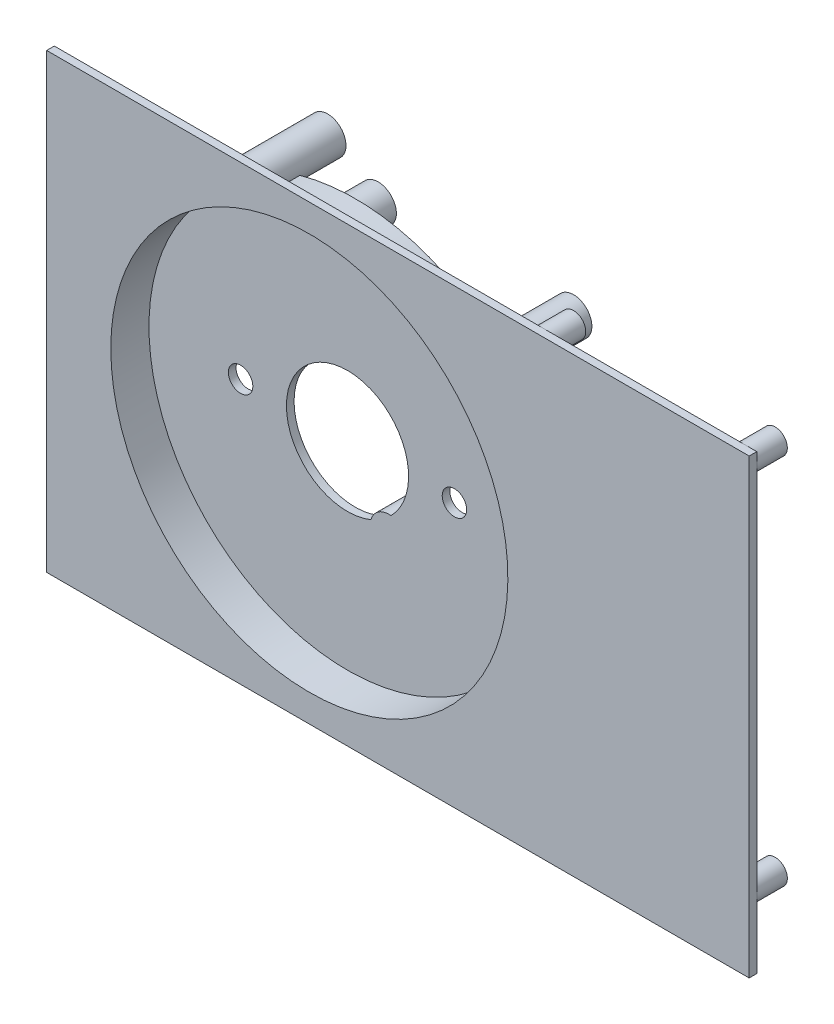
SolidWorks part; units mm, degrees
ref_plane "Front Plane" through (0, 0, 0) normal (0, 0, 1) x (1, 0, 0)
ref_plane "Top Plane" through (0, 0, 0) normal (0, 1, 0) x (1, 0, 0)
ref_plane "Right Plane" through (0, 0, 0) normal (1, 0, 0) x (0, 0, -1)
sketch "Sketch1" plane through (0, 0, 7.9375) normal (0, 0, -1) x (-1, 0, 0)
  line L1 (54.61, -46.99) -> (-91.44, -46.99)
  line L2 (54.61, -46.99) -> (54.61, 46.99)
  line L3 (54.61, 46.99) -> (-91.44, 46.99)
  line L4 (-91.44, -46.99) -> (-91.44, 46.99)
  circle A0 centre (0, 0) radius 7.9336 construction
  circle A1 centre (0, 0) radius 12.7 construction
  circle A2 centre (0, 0) radius 41.275 construction
  circle A3 centre (0, 0) radius 41.275
  point P10 (-91.44, 0)
  dimension "D3" = 146.05
  dimension "D1" = 91.44
  dimension "D2" = 93.98
extrude "main" add sketch "Sketch1" along normal blind 1.5875
sketch "Sketch2" plane through (0, 0, 0) normal (0, 0, -1) x (-1, 0, 0)
  circle A0 centre (0, 0) radius 41.275
  circle A1 centre (0, 0) radius 41.275 construction
  circle A2 centre (22.225, 0) radius 2.54
  circle A3 centre (-22.225, 0) radius 2.54
  circle A4 centre (22.225, 0) radius 2.54 construction
  circle A5 centre (-22.225, 0) radius 2.54 construction
  circle A6 centre (0, 0) radius 12.7
  circle A7 centre (0, 0) radius 12.7 construction
extrude "disk top" add sketch "Sketch2" along normal blind 1.5875 separate body
sketch "Sketch3" plane through (0, 0, -1.5875) normal (0, 0, -1) x (-1, 0, 0)
  circle A0 centre (0, 0) radius 41.275 construction
  circle A1 centre (0, 0) radius 41.275
  circle A2 centre (0, 0) radius 42.8625
  dimension "D1" = 1.5875
extrude "raised disk" add sketch "Sketch3" against normal up to next
sketch "Sketch4" plane through (0, 0, 6.35) normal (0, 0, -1) x (-1, 0, 0)
  circle A0 centre (15.24, 41.91) radius 3.81
  circle A1 centre (15.24, -44.45) radius 3.81
  circle A2 centre (15.24, -44.45) radius 1.524 construction
  circle A3 centre (15.24, 41.91) radius 1.524 construction
  circle A4 centre (15.24, -44.45) radius 1.224
  circle A5 centre (15.24, 41.91) radius 1.224
  dimension "D1" = 7.62
  dimension "D2" = 2.4479
extrude "SS relay mounting posts" add sketch "Sketch4" along normal up to surface (17.4625 mm away)
sketch "Sketch5" plane through (0, 0, 6.35) normal (0, 0, -1) x (-1, 0, 0)
  circle A0 centre (-46.99, 44.45) radius 2.54
  circle A1 centre (-46.99, 44.45) radius 1.1906
  circle A2 centre (-88.9, 44.45) radius 1.1906
  circle A3 centre (-88.9, 44.45) radius 2.54
  circle A4 centre (-46.99, 24.13) radius 2.54
  circle A5 centre (-46.99, 24.13) radius 1.1906
  circle A6 centre (-46.99, -33.02) radius 2.54
  circle A7 centre (-46.99, -33.02) radius 1.1906
  circle A8 centre (-88.9, -33.02) radius 2.54
  circle A9 centre (-88.9, -33.02) radius 1.1906
  dimension "D1" = 5.08
  dimension "D2" = 2.3813
extrude "mech relay mounting posts" add sketch "Sketch5" along normal up to surface (6.35 mm away)
sketch "Sketch6" plane through (0, 0, -7.9375) normal (0, 0, 1) x (1, 0, 0)
  circle A0 centre (39.0525, 38.1) radius 3.81
  circle A1 centre (-1.5875, 38.1) radius 3.81
  circle A2 centre (8.5725, -12.7) radius 3.81
  circle A3 centre (39.0525, -12.7) radius 3.81
  circle A4 centre (39.0525, 38.1) radius 1.524 construction
  circle A5 centre (39.0525, -12.7) radius 1.524 construction
  circle A6 centre (-1.5875, 38.1) radius 1.524 construction
  circle A7 centre (8.5725, -12.7) radius 1.524 construction
  circle A8 centre (-1.5875, 38.1) radius 1.1906
  circle A9 centre (39.0525, 38.1) radius 1.1906
  circle A10 centre (39.0525, -12.7) radius 1.1906
  circle A11 centre (8.5725, -12.7) radius 1.1906
  dimension "D1" = 7.62
  dimension "D2" = 2.3813
extrude "Arduino mounting 1" add sketch "Sketch6" along normal up to surface (7.9375 mm away) up to face at (0.0837, -0.2303, 0)
sketch "Sketch7" plane through (0, 0, 6.35) normal (0, 0, -1) x (-1, 0, 0)
  line L0 (-39.5699, -16.4747) -> (-41.6912, -9.9517)
  circle A0 centre (-39.0525, 38.1) radius 3.81 construction
  circle A4 centre (-39.0525, 38.1) radius 3.81
  arc A8 (-41.6912, -9.9517) -> (-39.5699, -16.4747) centre (-39.0525, -12.7) ccw construction
  arc A12 (-41.6912, -9.9517) -> (-39.5699, -16.4747) centre (-39.0525, -12.7) ccw
extrude "Arduino mounting 2" add sketch "Sketch7" along normal up to surface (6.35 mm away) up to face at (37.8619, 38.1, 0)
